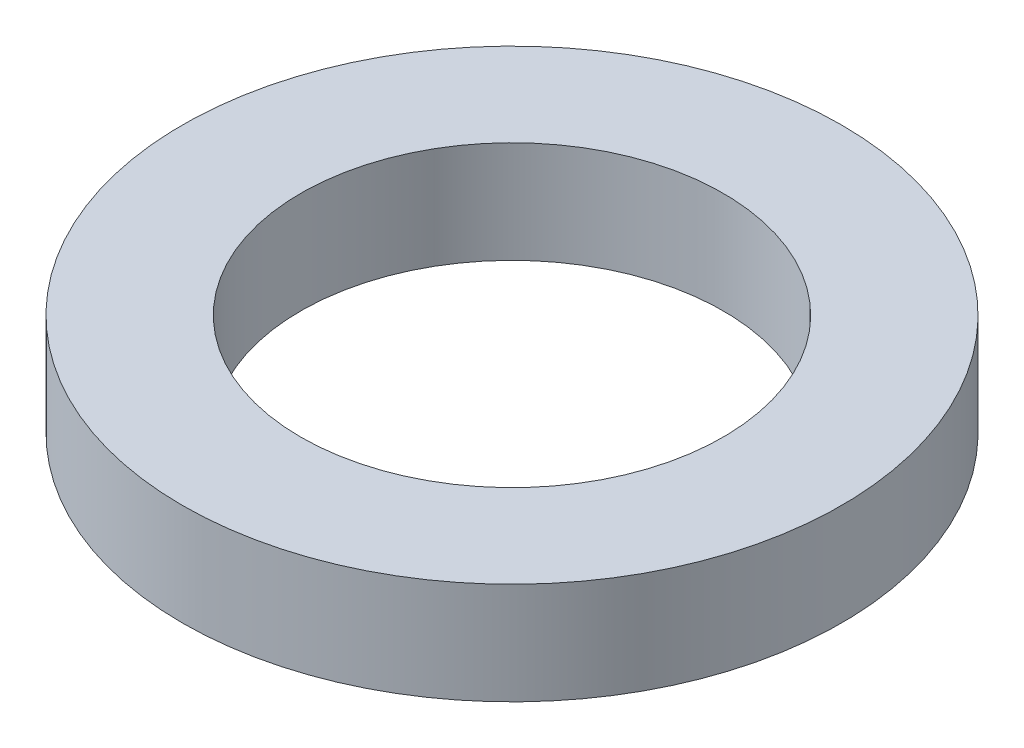
SolidWorks part; units mm, degrees
material "ABS"
ref_plane "前视基准面" through (0, 0, 0) normal (0, 0, 1) x (1, 0, 0)
ref_plane "上视基准面" through (0, 0, 0) normal (0, 1, 0) x (1, 0, 0)
ref_plane "右视基准面" through (0, 0, 0) normal (1, 0, 0) x (0, 0, -1)
other "Configuration Table"
sketch "草图1" plane through (0, 0, 0) normal (0, 1, 0) x (1, 0, 0)
  circle A0 centre (0, 0) radius 7.05
  circle A1 centre (0, 0) radius 11
  dimension "D1" = 14.1
  dimension "D2" = 22
extrude "凸台-拉伸1" add sketch "草图1" along normal blind 3.4
